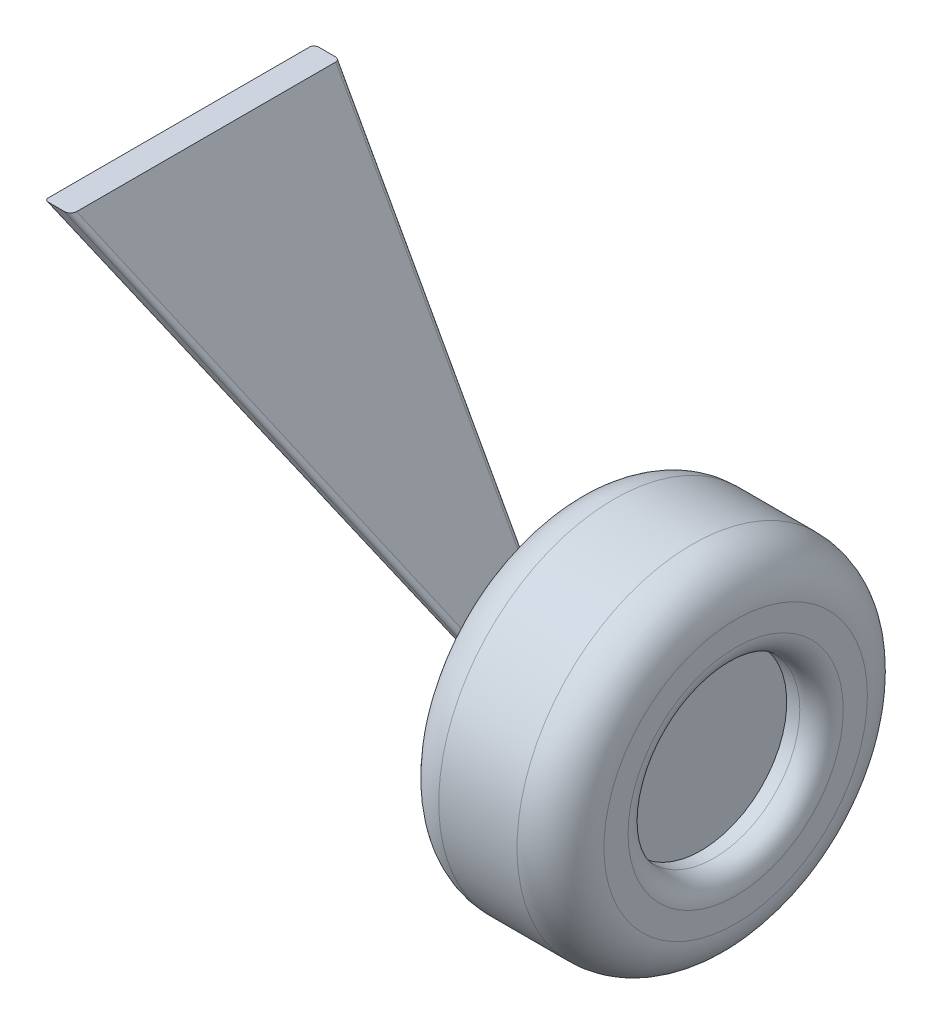
SolidWorks part; units mm, degrees
ref_plane "Front Plane" through (0, 0, 0) normal (0, 0, 1) x (1, 0, 0)
ref_plane "Top Plane" through (0, 0, 0) normal (0, 1, 0) x (1, 0, 0)
ref_plane "Right Plane" through (0, 0, 0) normal (1, 0, 0) x (0, 0, -1)
sketch "Sketch1" plane through (0, 0, 0) normal (1, 0, 0) x (0, 0, -1)
  circle A0 centre (0, 0) radius 201.5
  circle A2 centre (0, 0) radius 98.7681
  dimension "D1" = 403
extrude "Boss-Extrude1" add sketch "Sketch1" along normal blind 190
sketch "Sketch2" plane through (0, 0, 0) normal (-1, 0, 0) x (0, 0, 1)
  circle A1 centre (0, 0) radius 98.7681
extrude "Boss-Extrude2" add sketch "Sketch2" against normal blind 150
fillet "Fillet1" radius 50 2 edges at (190, 0, -201.5) (0, 0, -201.5)
fillet "Fillet2" radius 25 1 edges at (190, 0, -98.7681)
ref_plane "Plane1" through (-300, 0, 0) normal (-1, 0, 0) x (0, 0, 1)
sketch "Sketch3" plane through (0, 0, 0) normal (0, 0, 1) x (1, 0, 0)
  line L3 (0, 151.5) -> (0, -151.5) construction
  line L4 (0, -30) -> (0, 0)
  line L5 (0, 0) -> (-265, 481.9492)
  line L6 (-265, 481.9492) -> (-295, 481.9492)
  line L7 (-295, 481.9492) -> (0, -30)
  dimension "D1" = 30
  dimension "D2" = 30
  dimension "D3" = 550
  dimension "D4" = 265
extrude "Boss-Extrude3" add sketch "Sketch3" along normal blind 310
sketch "Sketch4" plane through (-300, 0, 0) normal (-1, 0, 0) x (0, 0, 1)
  line L0 (40, -30) -> (310, 481.9492)
  line L1 (148.5, -30) -> (0, -30) construction
  line L2 (310, 481.9492) -> (310, -30)
  line L3 (310, -30) -> (40, -30)
  line L4 (0, -30) -> (0, 0) construction
  dimension "D1" = 40
extrude "Cut-Extrude1" cut sketch "Sketch4" against normal blind 300
fillet "Fillet3" radius 5 4 edges at (-147.5, 225.9746, 175) (-147.5, 225.9746, 0) (-132.5, 240.9746, 182.9109) (-132.5, 240.9746, 0)
